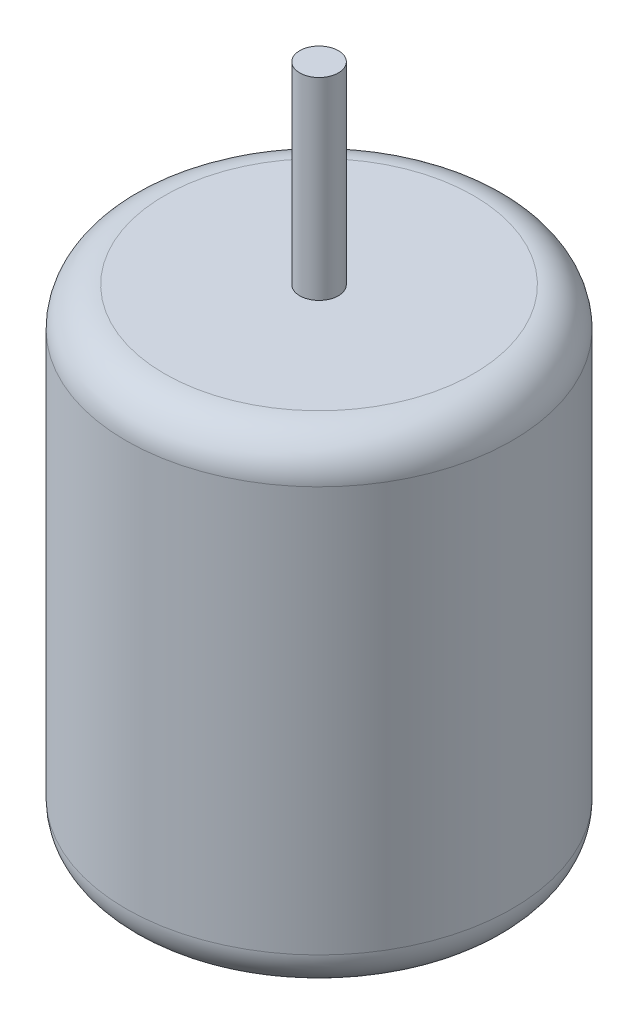
SolidWorks part; units mm, degrees
ref_plane "Front Plane" through (0, 0, 0) normal (0, 0, 1) x (1, 0, 0)
ref_plane "Top Plane" through (0, 0, 0) normal (0, 1, 0) x (1, 0, 0)
ref_plane "Right Plane" through (0, 0, 0) normal (1, 0, 0) x (0, 0, -1)
sketch "Sketch1" plane through (0, 0, 0) normal (0, 1, 0) x (1, 0, 0)
  circle A0 centre (0, 0) radius 10
  dimension "D1" = 20
extrude "Boss-Extrude1" add sketch "Sketch1" along normal blind 25
sketch "Sketch2" plane through (0, 25, 0) normal (0, 1, 0) x (1, 0, 0)
  circle A0 centre (0, 0) radius 1
extrude "Boss-Extrude2" add sketch "Sketch2" along normal blind 10
fillet "Fillet1" radius 2 2 edges at (0, 0, 10) (0, 25, 10)
